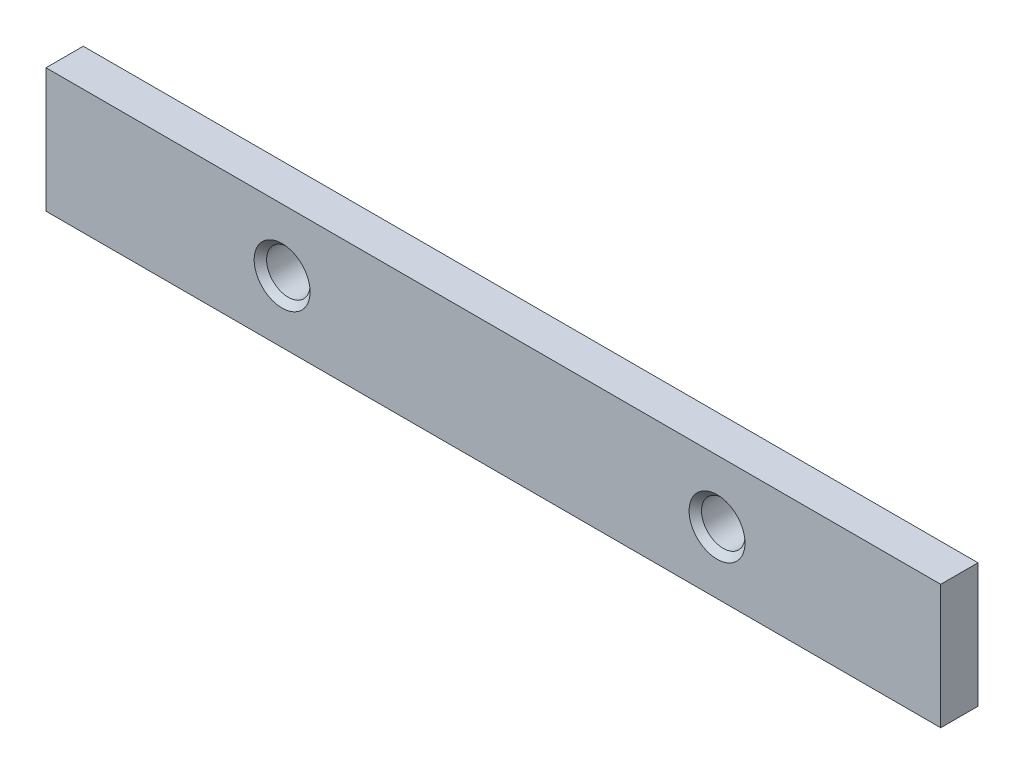
SolidWorks part; units mm, degrees
ref_plane "Front Plane" through (0, 0, 0) normal (0, 0, 1) x (1, 0, 0)
ref_plane "Top Plane" through (0, 0, 0) normal (0, 1, 0) x (1, 0, 0)
ref_plane "Right Plane" through (0, 0, 0) normal (1, 0, 0) x (0, 0, -1)
sketch "Sketch1" plane through (0, 0, 0) normal (0, 0, 1) x (1, 0, 0)
  line L1 (-72, 10) -> (72, 10)
  line L2 (-72, 10) -> (-72, -10)
  line L3 (-72, -10) -> (72, -10)
  line L4 (72, 10) -> (72, -10)
  line L5 (-72, 10) -> (72, -10) construction
  line L6 (-72, -10) -> (72, 10) construction
  point P0 (0, 0)
  dimension "D1" = 20
  dimension "D2" = 144
extrude "Boss-Extrude1" add sketch "Sketch1" along normal blind 6
hole_wizard "CSK for M1.6 Countersunk Flat Head Screw1" positions "Sketch2" profile "Sketch3" countersink size "M1.6" standard "ISO" end condition through all
sketch "Sketch2" plane through (0, 0, 6) normal (0, 0, 1) x (1, 0, 0)
  line L0 (-72, 10) -> (-72, -10) construction
  point P0 (-34, 0)
  point P2 (36, 0)
  point P7 (-72, 0)
  dimension "D1" = 70
  dimension "D2" = 38
sketch "Sketch3" plane through (-34, 0, 6) normal (1, 0, 0) x (0, -1, 0)
  line L0 (0, 0) -> (0, 6)
  line L1 (0, 6) -> (3.5, 6)
  line L2 (3.5, 6) -> (3.5, 1)
  line L3 (3.5, 1) -> (4.5, 0)
  line L5 (4.5, 0) -> (0, 0)
  line L6 (-3.5, 1) -> (-4.5, 0) construction
  line L11 (0, -6.35) -> (0, 107.95) construction
  dimension "Thru Hole Dia." = 7
  dimension "Thru Hole Depth" = 6
  dimension "Near C'Sink Dia." = 9
  dimension "Near C'Sink Angle" = 90
